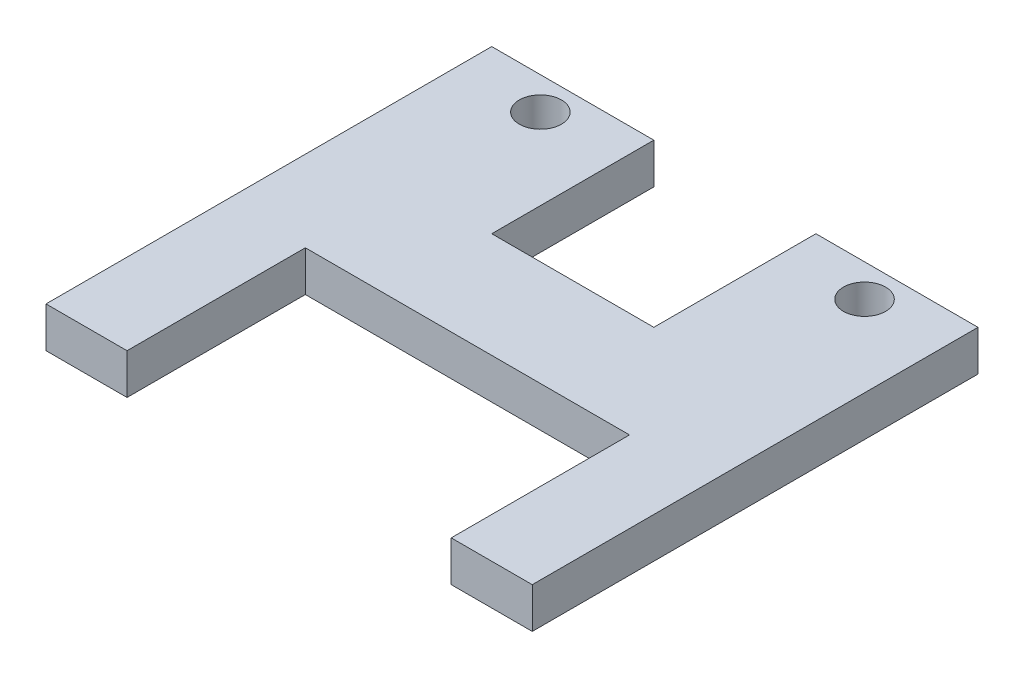
SolidWorks part; units mm, degrees
ref_plane "Front Plane" through (0, 0, 0) normal (0, 0, 1) x (1, 0, 0)
ref_plane "Top Plane" through (0, 0, 0) normal (0, 1, 0) x (1, 0, 0)
ref_plane "Right Plane" through (0, 0, 0) normal (1, 0, 0) x (0, 0, -1)
sketch "Sketch1" plane through (0, 0, 0) normal (0, 1, 0) x (1, 0, 0)
  line L1 (-38.1, 34.925) -> (38.1, 34.925)
  line L2 (-38.1, 34.925) -> (-38.1, -34.925)
  line L3 (-38.1, -34.925) -> (38.1, -34.925)
  line L4 (38.1, 34.925) -> (38.1, -34.925)
  line L5 (-38.1, 34.925) -> (38.1, -34.925) construction
  line L6 (-38.1, -34.925) -> (38.1, 34.925) construction
  point P0 (0, 0)
  dimension "D1" = 76.2
  dimension "D2" = 69.85
extrude "Boss-Extrude1" add sketch "Sketch1" along normal mid plane 6.35
sketch "Sketch2" plane through (0, 3.175, 0) normal (0, 1, 0) x (1, 0, 0)
  line L0 (-38.1, -34.925) -> (38.1, -34.925) construction
  line L1 (-25.4, -34.925) -> (25.4, -34.925)
  line L2 (-25.4, -34.925) -> (-25.4, -6.985)
  line L3 (-25.4, -6.985) -> (25.4, -6.985)
  line L4 (25.4, -34.925) -> (25.4, -6.985)
  line L5 (38.1, -34.925) -> (38.1, 34.925) construction
  line L6 (-38.1, 34.925) -> (-38.1, -34.925) construction
  dimension "D1" = 12.7
  dimension "D2" = 12.7
  dimension "D3" = 27.94
extrude "Cut-Extrude1" cut sketch "Sketch2" against normal through all
sketch "Sketch4" plane through (0, 3.175, 0) normal (0, 1, 0) x (1, 0, 0)
  line L0 (38.1, 34.925) -> (-38.1, 34.925) construction
  circle A0 centre (-25.4, 29.845) radius 3.302
  circle A1 centre (25.4, 29.845) radius 3.302
  dimension "D1" = 50.8
  dimension "D2" = 25.4
  dimension "D3" = 5.08
extrude "Cut-Extrude2" cut sketch "Sketch4" against normal through all
sketch "Sketch5" plane through (0, 3.175, 0) normal (0, 1, 0) x (1, 0, 0)
  line L0 (38.1, 34.925) -> (-38.1, 34.925) construction
  line L1 (-12.7, 34.925) -> (12.7, 34.925)
  line L2 (-12.7, 34.925) -> (-12.7, 9.525)
  line L3 (-12.7, 9.525) -> (12.7, 9.525)
  line L4 (12.7, 34.925) -> (12.7, 9.525)
  line L5 (-38.1, 34.925) -> (-38.1, -34.925) construction
  line L6 (38.1, -34.925) -> (38.1, 34.925) construction
  dimension "D1" = 25.4
  dimension "D2" = 25.4
  dimension "D3" = 25.4
extrude "Cut-Extrude3" cut sketch "Sketch5" against normal through all
